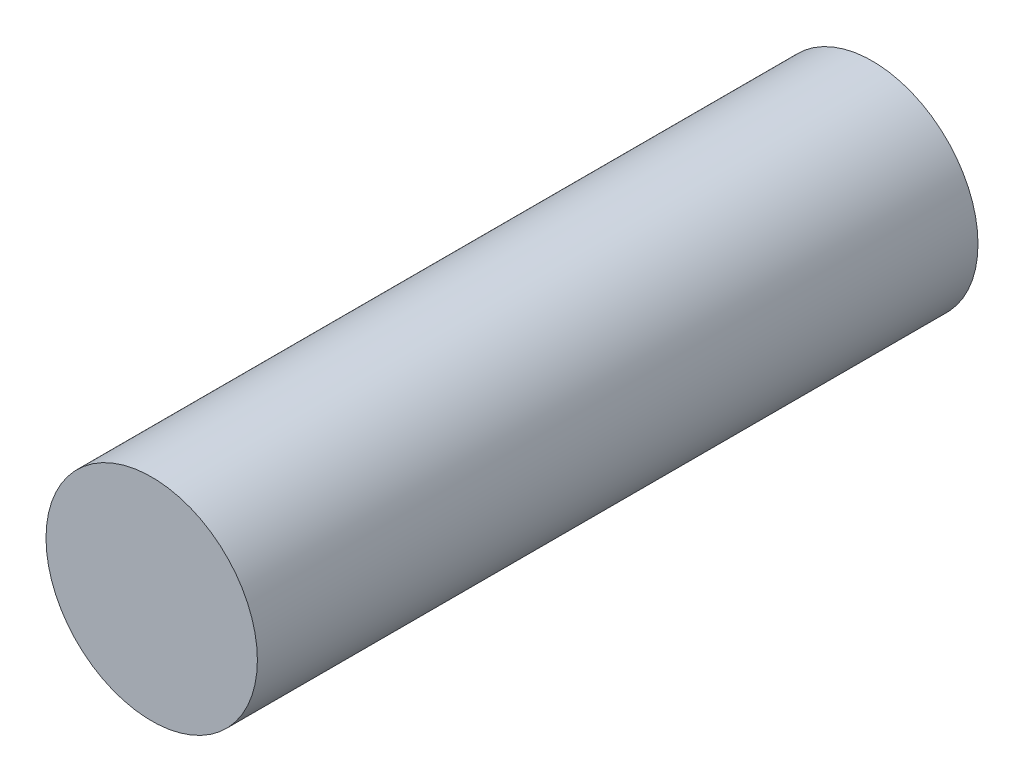
SolidWorks part; units mm, degrees
ref_plane "Спереди" through (0, 0, 0) normal (0, 0, 1) x (1, 0, 0)
ref_plane "Сверху" through (0, 0, 0) normal (0, 1, 0) x (1, 0, 0)
ref_plane "Справа" through (0, 0, 0) normal (1, 0, 0) x (0, 0, -1)
sketch "Эскиз1" plane through (0, 0, 0) normal (0, 0, 1) x (1, 0, 0)
  circle A0 centre (0, 0) radius 2.2
  dimension "D1" = 4.4
extrude "Бобышка-Вытянуть1" add sketch "Эскиз1" along normal blind 15
